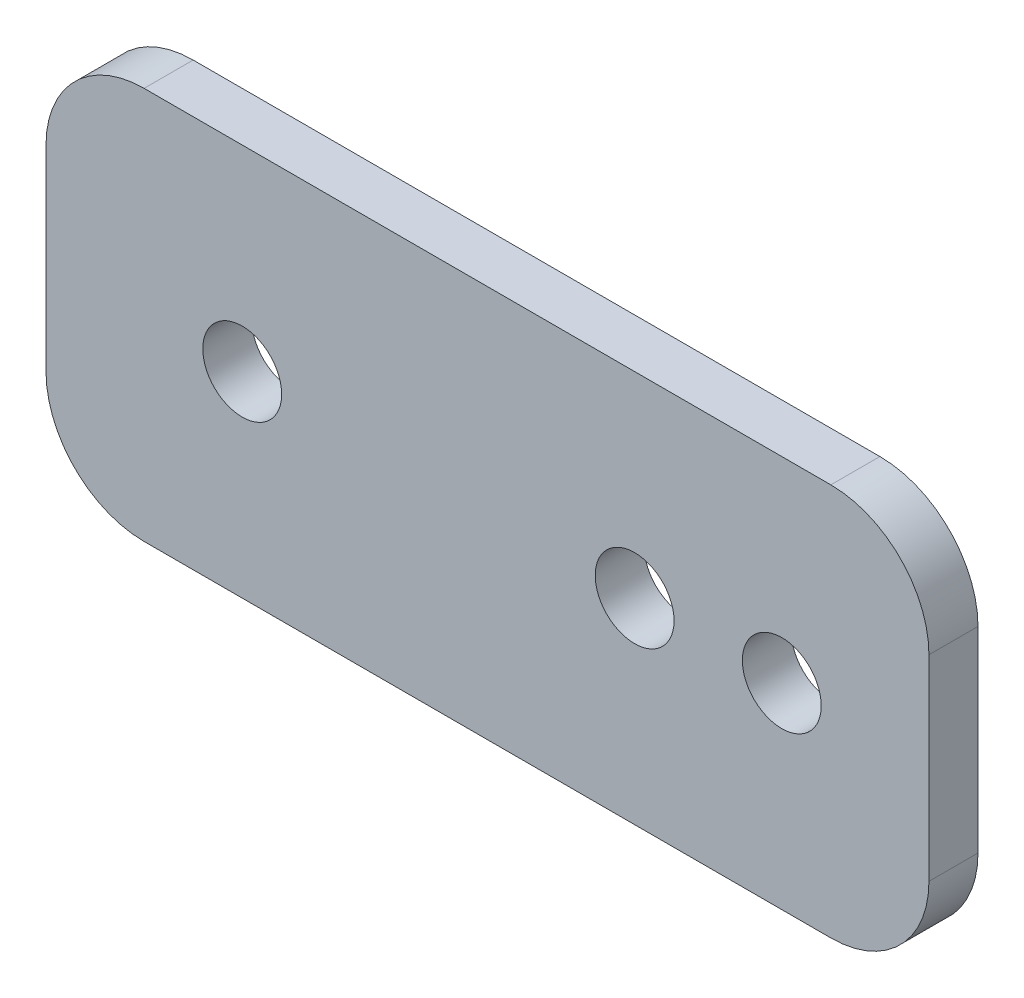
SolidWorks part; units mm, degrees
material "6061-T6 (SS)"
ref_plane "Front Plane" through (0, 0, 0) normal (0, 0, 1) x (1, 0, 0)
ref_plane "Top Plane" through (0, 0, 0) normal (0, 1, 0) x (1, 0, 0)
ref_plane "Right Plane" through (0, 0, 0) normal (1, 0, 0) x (0, 0, -1)
sketch "Sketch1" plane through (0, 0, 0) normal (0, 0, 1) x (1, 0, 0)
  line L0 (12.7, -12.7) -> (38.1, -12.7) construction
  line L1 (0, 0) -> (57.15, 0)
  line L2 (0, 0) -> (0, -25.4)
  line L3 (0, -25.4) -> (57.15, -25.4)
  line L4 (57.15, 0) -> (57.15, -25.4)
  circle A0 centre (12.7, -12.7) radius 2.5527
  circle A1 centre (38.1, -12.7) radius 2.5527
  circle A3 centre (47.625, -12.7) radius 2.5527
  point P10 (0, -12.7)
  dimension "D3" = 5.1054
  dimension "D4" = 25.4
  dimension "D5" = 12.7
  dimension "D1" = 57.15
  dimension "D2" = 25.4
  dimension ".5" = 9.525
extrude "Boss-Extrude1" add sketch "Sketch1" along normal blind 3.175
fillet "Fillet1" radius 6.35 4 edges at (0, -25.4, 1.5875) (57.15, -25.4, 1.5875) (57.15, 0, 1.5875) (0, 0, 1.5875)
